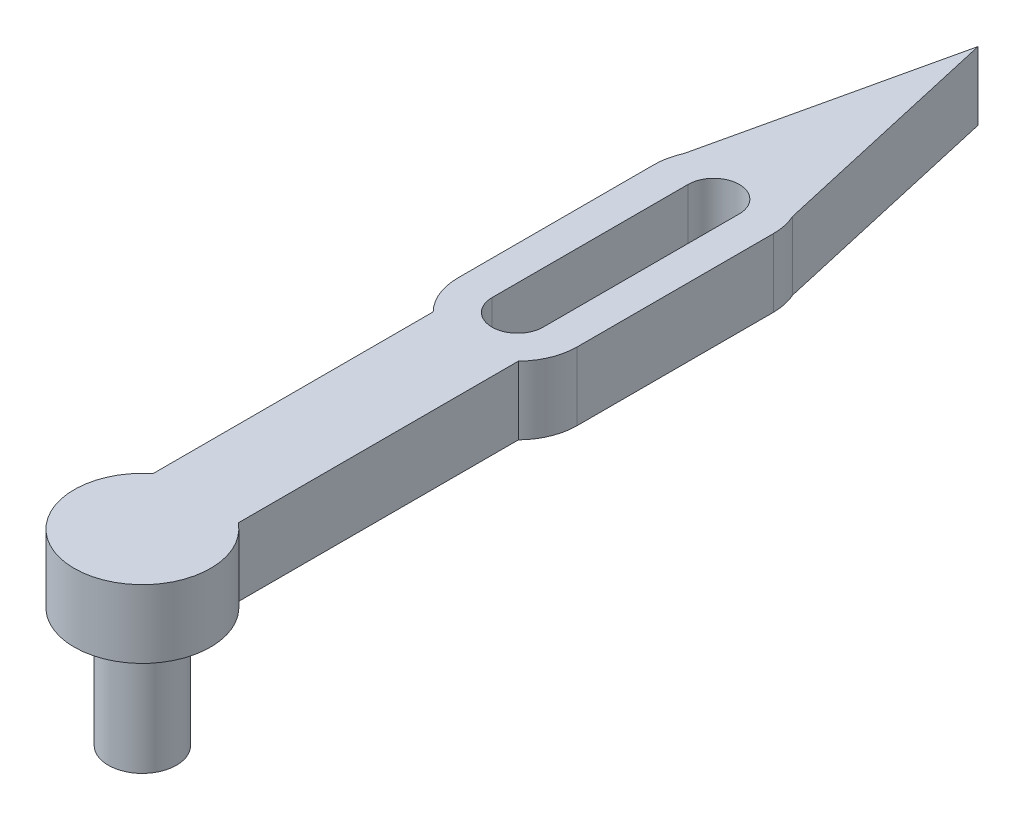
SolidWorks part; units mm, degrees
material "AISI 1020"
ref_plane "Alzado" through (0, 0, 0) normal (0, 0, 1) x (1, 0, 0)
ref_plane "Planta" through (0, 0, 0) normal (0, 1, 0) x (1, 0, 0)
ref_plane "Vista lateral" through (0, 0, 0) normal (1, 0, 0) x (0, 0, -1)
sketch "Sketch2" plane through (0, 0, 0) normal (0, 1, 0) x (1, 0, 0)
  line L1 (-5, 6.245) -> (-5, 39.101)
  line L2 (0, 0) -> (0, 116.2239) construction
  line L3 (-3, 67) -> (-3, 44)
  line L4 (-7, 44) -> (-7, 67)
  line L5 (-6.378, 69.8846) -> (0, 98)
  line L6 (3, 67) -> (3, 44)
  line L7 (5, 6.245) -> (5, 39.101)
  line L8 (0, 116.2239) -> (0, 98) construction
  line L9 (7, 44) -> (7, 67)
  line L10 (6.378, 69.8846) -> (0, 98)
  arc A0 (-5, 6.245) -> (5, 6.245) centre (0, 0) ccw
  arc A1 (3, 67) -> (-3, 67) centre (0, 67) ccw
  arc A2 (-3, 44) -> (3, 44) centre (0, 44) ccw
  arc A3 (-7, 67) -> (-6.378, 69.8846) centre (0, 67) cw
  arc A4 (-7, 44) -> (-5, 39.101) centre (0, 44) ccw
  arc A5 (7, 44) -> (5, 39.101) centre (0, 44) cw
  arc A6 (7, 67) -> (6.378, 69.8846) centre (0, 67) ccw
  dimension "D1" = 16
  dimension "D2" = 6
  dimension "D4" = 6
  dimension "D3" = 98
  dimension "D5" = 44
  dimension "D6" = 5
  dimension "D7" = 67
  dimension "D8" = 4
extrude "Boss-Extrude1" add sketch "Sketch2" along normal blind 8
sketch "Sketch3" plane through (0, 0, 0) normal (0, -1, 0) x (1, 0, 0)
  circle A0 centre (0, 0) radius 4
  dimension "D1" = 8
extrude "Boss-Extrude2" add sketch "Sketch3" along normal blind 14
